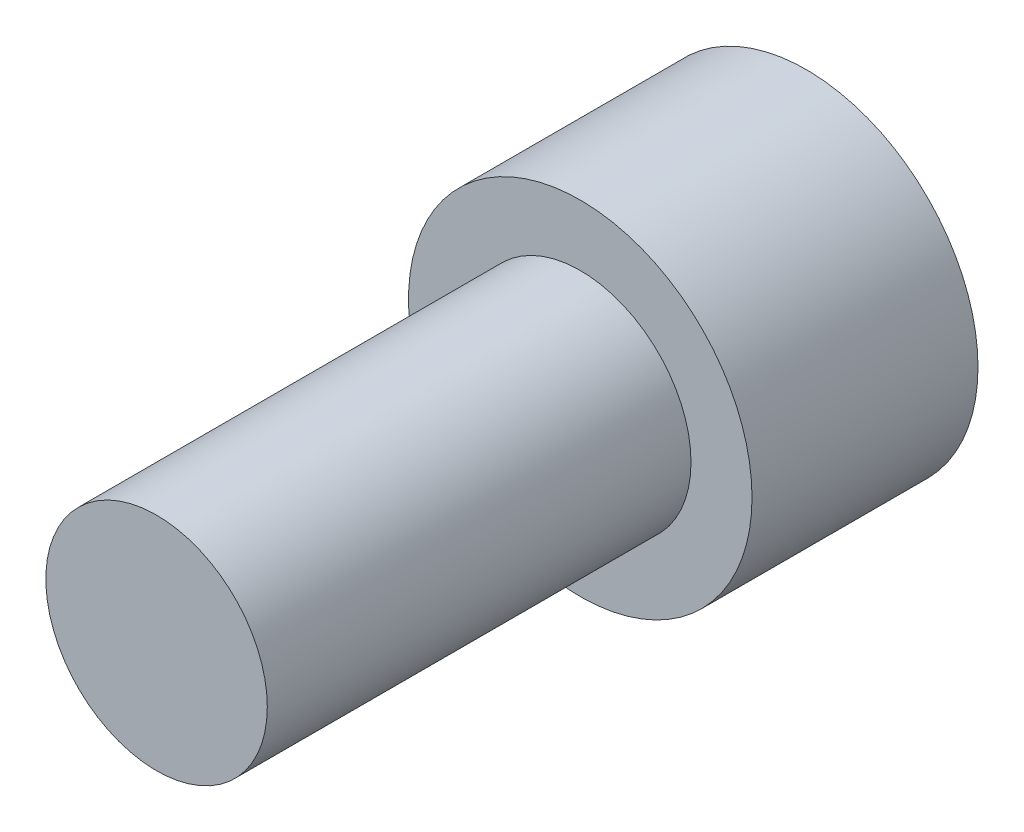
SolidWorks part; units mm, degrees
ref_plane "Front Plane" through (0, 0, 0) normal (0, 0, 1) x (1, 0, 0)
ref_plane "Top Plane" through (0, 0, 0) normal (0, 1, 0) x (1, 0, 0)
ref_plane "Right Plane" through (0, 0, 0) normal (1, 0, 0) x (0, 0, -1)
sketch "Sketch1" plane through (0, 0, 0) normal (0, 0, 1) x (1, 0, 0)
  circle A0 centre (0, 0) radius 3.8608
extrude "Extrude1" add sketch "Sketch1" along normal blind 14.605
sketch "Sketch2" plane through (0, 0, 14.605) normal (0, 0, 1) x (1, 0, 0)
  circle A0 centre (0, 0) radius 2.4892
extrude "Extrude2" cut sketch "Sketch2" against normal blind 9.525 flip side to cut
sketch "Sketch3" plane through (0, 0, 0) normal (0, 0, -1) x (-1, 0, 0)
  line L1 (0, 2.9877) -> (-2.5874, 1.4938)
  line L2 (-2.5874, 1.4938) -> (-2.5874, -1.4938)
  line L3 (-2.5874, -1.4938) -> (0, -2.9877)
  line L4 (0, -2.9877) -> (2.5874, -1.4938)
  line L5 (2.5874, -1.4938) -> (2.5874, 1.4938)
  line L6 (2.5874, 1.4938) -> (0, 2.9877)
  circle A0 centre (0, 0) radius 2.5874 construction
extrude "Extrude3" cut sketch "Sketch3" against normal blind 3.048
